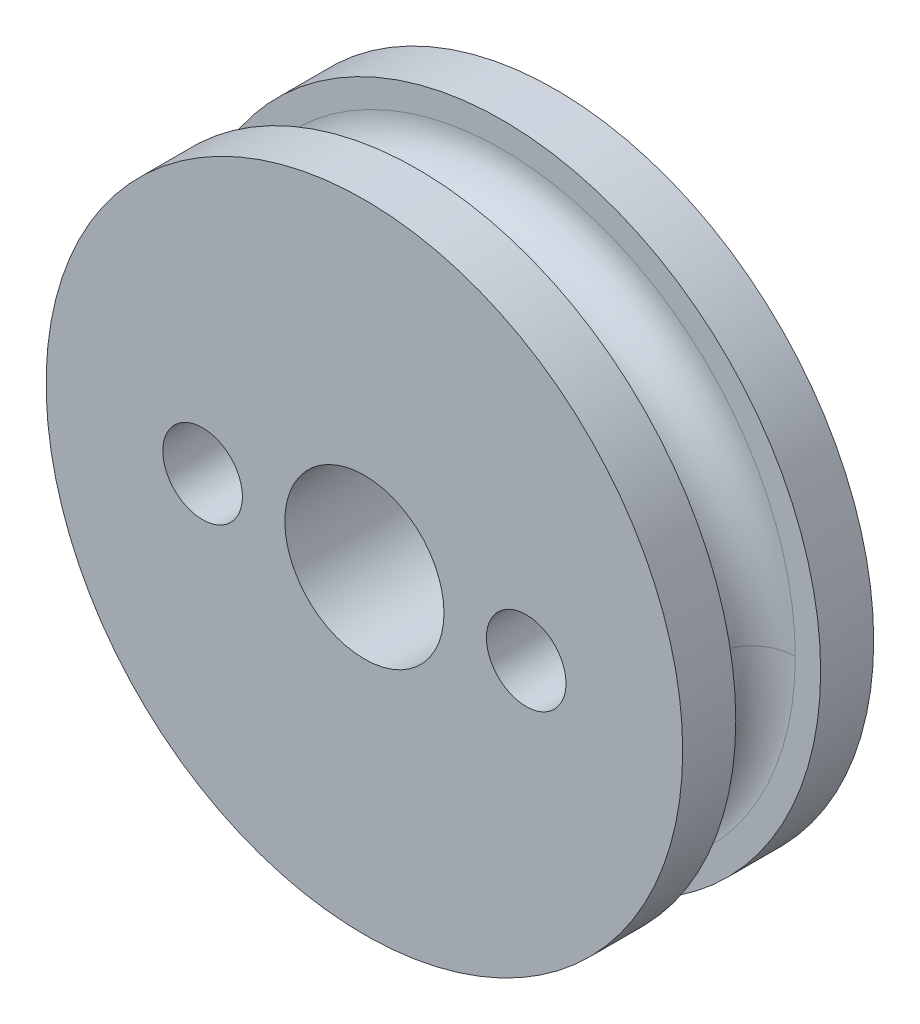
SolidWorks part; units mm, degrees
ref_plane "正面" through (0, 0, 0) normal (0, 0, 1) x (1, 0, 0)
ref_plane "平面" through (0, 0, 0) normal (0, 1, 0) x (1, 0, 0)
ref_plane "右側面" through (0, 0, 0) normal (1, 0, 0) x (0, 0, -1)
sketch "ｽｹｯﾁ1" plane through (0, 0, 0) normal (0, 0, 1) x (1, 0, 0)
  circle A0 centre (0, 0) radius 12
  dimension "D1" = 24
extrude "ﾎﾞｽ - 押し出し1" add sketch "ｽｹｯﾁ1" along normal blind 2 contours A0
sketch "ｽｹｯﾁ2" plane through (0, 0, 2) normal (0, 0, 1) x (1, 0, 0)
  circle A0 centre (0, 0) radius 11
  dimension "D1" = 22
extrude "ﾎﾞｽ - 押し出し2" add sketch "ｽｹｯﾁ2" along normal blind 3.2
sketch "ｽｹｯﾁ3" plane through (0, 0, 5.2) normal (0, 0, 1) x (1, 0, 0)
  circle A0 centre (0, 0) radius 12
  dimension "D1" = 24
extrude "ﾎﾞｽ - 押し出し3" add sketch "ｽｹｯﾁ3" along normal blind 2 contours A0
sketch "ｽｹｯﾁ4" plane through (0, 0, 0) normal (0, 0, -1) x (-1, 0, 0)
  circle A0 centre (0, 0) radius 3
  dimension "D1" = 6
extrude "ｶｯﾄ - 押し出し1" cut sketch "ｽｹｯﾁ4" against normal blind 30
sketch "ｽｹｯﾁ5" plane through (0, 0, 0) normal (0, 0, -1) x (-1, 0, 0)
  line L0 (0, 0) -> (6.1, 0)
  line L1 (0, 0) -> (-6.1, 0)
  circle A0 centre (-6.1, 0) radius 1.5
  circle A1 centre (6.1, 0) radius 1.5
  dimension "D3" = 3
  dimension "D4" = 3
  dimension "D1" = 6.1
  dimension "D2" = 6.1
extrude "ｶｯﾄ - 押し出し4" cut sketch "ｽｹｯﾁ5" against normal through all
sketch "ｽｹｯﾁ7" plane through (0, 0, 0) normal (0, 0, -1) x (-1, 0, 0)
  circle A0 centre (-6.1, 0) radius 3
  circle A1 centre (6.1, 0) radius 3
  dimension "D1" = 6
  dimension "D2" = 6
sketch3d "3Dｽｹｯﾁ2"
  line L0 (-11, 0, 5.2) -> (-11, 0, 3.5997)
  circle A0 centre (0, 0, 5.2) radius 11 construction
  circle A1 centre (-11, 0, 3.5997) radius 1.6003
  point P4 (0, 0, 16.2)
  point P6 (-11, 1.6003, 3.5997)
sweep "ｶｯﾄ - ｽｲｰﾌﾟ2" cut profiles "3Dｽｹｯﾁ2" path edge at (11, 0, 5.2)
extrude "ｶｯﾄ - 押し出し9" cut sketch "ｽｹｯﾁ7" against normal blind 4
